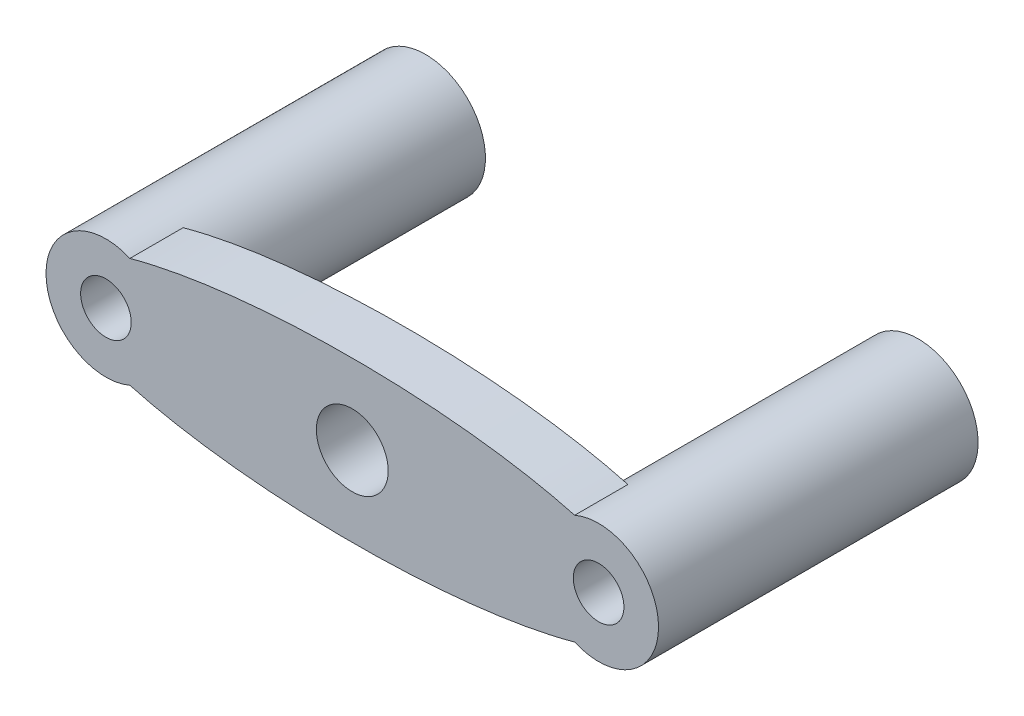
SolidWorks part; units mm, degrees
ref_plane "Front Plane" through (0, 0, 0) normal (0, 0, 1) x (1, 0, 0)
ref_plane "Top Plane" through (0, 0, 0) normal (0, 1, 0) x (1, 0, 0)
ref_plane "Right Plane" through (0, 0, 0) normal (1, 0, 0) x (0, 0, -1)
sketch "Sketch1" plane through (0, 0, 0) normal (0, 0, 1) x (1, 0, 0)
  line L0 (-23.495, 0) -> (23.495, 0) construction
  circle A0 centre (-23.495, 0) radius 2.413
  circle A1 centre (0, 0) radius 3.429
  circle A2 centre (23.495, 0) radius 2.413
  arc A3 (21.2113, -5.2389) -> (21.2113, 5.2389) centre (23.495, 0) ccw
  arc A4 (-21.2113, 5.2389) -> (-21.2113, -5.2389) centre (-23.495, 0) ccw
  ellipse E0 centre (0, 0) end of major axis (-29.21, 0) minor radius 7.62 (21.2113, 5.2389) -> (-21.2113, 5.2389) ccw
  ellipse E1 centre (0, 0) end of major axis (-29.21, 0) minor radius 7.62 (-21.2113, -5.2389) -> (21.2113, -5.2389) ccw
  point P2 (0, 0)
  dimension "D1" = 4.826
  dimension "D3" = 6.858
  dimension "D2" = 46.99
  dimension "D4" = 15.24
  dimension "D5" = 58.42
extrude "Boss-Extrude1" add sketch "Sketch1" along normal blind 5.08
sketch "Sketch2" plane through (0, 0, 0) normal (0, 0, -1) x (-1, 0, 0)
  circle A0 centre (-23.495, 0) radius 5.715
  circle A1 centre (-23.495, 0) radius 2.413
  circle A2 centre (23.495, 0) radius 5.715
  circle A3 centre (23.495, 0) radius 2.413
  circle A4 centre (-23.495, 0) radius 2.413 construction
  ellipse E0 centre (0, 0) end of major axis (-29.21, 0) minor radius 7.62 construction
extrude "Boss-Extrude2" add sketch "Sketch2" along normal blind 25.4
